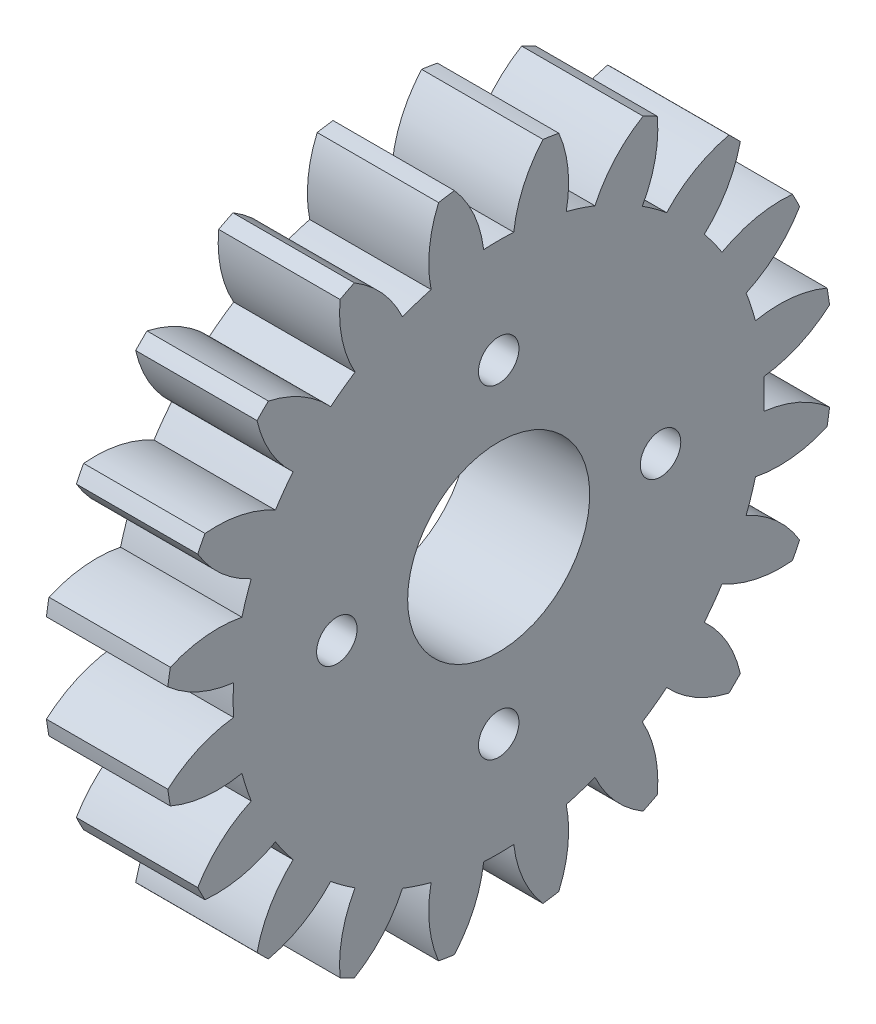
SolidWorks part; units mm, degrees
ref_plane "Plane1" through (0, 0, 0) normal (0, 0, 1) x (1, 0, 0)
ref_plane "Plane2" through (0, 0, 0) normal (0, 1, 0) x (1, 0, 0)
ref_plane "Plane3" through (0, 0, 0) normal (1, 0, 0) x (0, 0, -1)
sketch "HoldingSke" plane through (0, 0, 0) normal (0, 1, 0) x (1, 0, 0)
  line L0 (0, 0) -> (0.6265, -0.228)
  line L1 (-15, 0) -> (100, 0) construction
  line L2 (0, 0) -> (-2.1039, 2.3779)
  line L3 (0, 0) -> (-11.863, 4.5341)
  line L4 (0, 0) -> (8.1152, 2.9537)
  line L5 (0, 0) -> (-46.8476, -17.4728)
  line L6 (0, 0) -> (-4.9738, -3.3558)
  line L7 (-2.1039, 2.3779) -> (8.6586, 51.2059)
  line L8 (-76.2, 54.61) -> (-74.8, 54.61)
  line L9 (-71.009, 38.7566) -> (-53.1078, 45.2721)
  line L10 (-76.2, 71.12) -> (104.1128, 71.12)
  line L11 (0, 0) -> (-6, 0)
  line L12 (-76.2, 101.6) -> (-76.147, 101.6)
  line L13 (24.9733, 27.94) -> (52.9518, 28.4284)
  line L14 (24.9733, 27.94) -> (24.9743, 27.94)
  line L15 (24.9733, 27.94) -> (100.4006, 29.5858)
  line L16 (-63.627, -1.5) -> (-12.827, -1.5)
  circle A0 centre (0, 0) radius 4.5
  circle A1 centre (0, 0) radius 13.124
  circle A2 centre (0, 0) radius 37.5
  circle A3 centre (0, 0) radius 4.5
  dimension "MHD" = 26.248
  dimension "Hub_dia" = 75
  dimension "Bore" = 9
  dimension "MBD" = 9
  dimension "Num_teeth" = 20
  dimension "Pitch" = 0.6667
  dimension "Overall_len" = 50
  dimension "Show_teeth" = 20
  dimension "Thickness" = 6
  dimension "OAL" = 50.0001
  dimension "T_dim" = 1.4
  dimension "Ap" = 20
  dimension "H" = 19.05
  dimension "Pitch_radius" = 180.3128
  dimension "Width" = 6
  dimension "Backlash" = 0.053
  dimension "Addendum_fac" = 1
  dimension "Dedendum_fac" = 1.25
  dimension "Clearance_fac" = 0.25
  dimension "Dedendum_add" = 0.001
  dimension "Module" = 1.5
sketch "BasProSke" plane through (0, 0, 0) normal (0, 1, 0) x (1, 0, 0)
  line L0 (-10, 0) -> (60, 0) construction
  line L1 (0, 0) -> (0, 16.5)
  line L2 (0, 0) -> (6, 0)
  line L3 (6, 0) -> (6, 16.5)
  line L4 (6, 16.5) -> (0, 16.5)
  dimension "Thickness" = 6
  dimension "Diameter" = 33
revolve "Base-Revolve" add sketch "BasProSke" angle 360 about L0
sketch "TooCutSke" plane through (0, 0, 0) normal (1, 0, 0) x (0, 0, -1)
  line L1 (0, 0) -> (0, 107) construction
  line L2 (0, 0) -> (-1.2696, 14.9462) construction
  line L3 (0, 0) -> (-4.6808, 29.5532) construction
  line L4 (-1.2696, 14.9462) -> (-2.3404, 14.7766) construction
  arc A0 (0.7438, 13.1029) -> (-0.7438, 13.1029) centre (0, 0) ccw
  arc A1 (2.21, 16.377) -> (-2.21, 16.377) centre (0, 0) ccw
  circle A2 centre (0, 0) radius 15 construction
  circle A3 centre (0, 0) radius 14.0954 construction
  arc A4 (-0.7438, 13.1029) -> (-2.21, 16.377) centre (-6.7025, 12.3999) ccw
  arc A5 (2.21, 16.377) -> (0.7438, 13.1029) centre (6.7025, 12.3999) ccw
  dimension "Root_dia" = 26.248
  dimension "Overcut_dia" = 33.0508
  dimension "Pitch_dia" = 30
  dimension "Base_dia" = 28.1908
  dimension "Flank_rad" = 6
  dimension "Half_ang" = 9
  dimension "Half_CT" = 1.0841
extrude "ToothCut" cut sketch "TooCutSke" along normal through all
fillet "Breaks" [suppressed] radius 0.03
fillet "RootFillets" [suppressed] radius 0.376
pattern_circular "TeethCuts" count 20 every 18 about axis through (-10, 0, 0) along (1, 0, 0) of "ToothCut", "RootFillets", "Breaks"
sketch "HubNeaOneSke" plane through (0, 0, 0) normal (-1, 0, 0) x (0, 0, 1)
  circle A0 centre (0, 0) radius 13.124
  dimension "Diameter" = 26.248
extrude "HubNearOne" [suppressed] add sketch "HubNeaOneSke" along normal blind 44.0001
sketch "HubNeaBotSke" plane through (0, 0, 0) normal (-1, 0, 0) x (0, 0, 1)
  circle A0 centre (0, 0) radius 13.124
  dimension "Diameter" = 26.248
extrude "HubNearBoth" [suppressed] add sketch "HubNeaBotSke" along normal blind 22
ref_plane "FarPln" through (6, 0, 0) normal (1, 0, 0) x (0, 0, -1)
sketch "HubFarSke" plane through (6, 0, 0) normal (1, 0, 0) x (0, 0, -1)
  circle A0 centre (0, 0) radius 13.124
  dimension "Diameter" = 26.248
extrude "HubFar" [suppressed] add sketch "HubFarSke" along normal blind 22
sketch "BorSke" plane through (0, 0, 0) normal (1, 0, 0) x (0, 0, -1)
  circle A0 centre (0, 0) radius 4.5
  dimension "Diameter" = 9
extrude "Bore" cut sketch "BorSke" along normal mid plane 100.0001
sketch "KeySke" plane through (0, 0, 0) normal (1, 0, 0) x (0, 0, -1)
  line L0 (-1.5, 0) -> (-1.5, 5.9)
  line L1 (-1.5, 5.9) -> (1.5, 5.9)
  line L2 (1.5, 5.9) -> (1.5, 0)
  line L3 (0, 0) -> (0, 34) construction
  line L4 (-1.5, 0) -> (1.5, 0)
  dimension "Offset" = 5.9
  dimension "Width" = 3
extrude "Keyway" [suppressed] cut sketch "KeySke" along normal mid plane 100.0001
pattern_circular "Keyway2" [suppressed] count 2 every 90 about axis through (-10, 0, 0) along (1, 0, 0)
sketch "Esquisse1" plane through (6, 0, 0) normal (1, 0, 0) x (0, 0, -1)
  circle A0 centre (0, 0) radius 15
  dimension "D1" = 30
sketch "Esquisse2" plane through (6, 0, 0) normal (1, 0, 0) x (0, 0, -1)
  circle A0 centre (0, 0) radius 4 construction
  circle A1 centre (0, 0) radius 8 construction
  circle A2 centre (0, 8) radius 1
  circle A3 centre (8, 0) radius 1
  circle A4 centre (0, -8) radius 1
  circle A5 centre (-8, 0) radius 1
  dimension "D1" = 8
  dimension "D2" = 16
  dimension "D3" = 2
  dimension "D4" = 2
  dimension "D5" = 2
  dimension "D6" = 2
extrude "Enlèv. mat.-Extru.1" cut sketch "Esquisse2" against normal blind 6
equation "' \"Module@HoldingSke\" = 6.35"
equation "' \"Num_teeth@HoldingSke\" = 12"
equation "' \"Ap@HoldingSke\" =  20"
equation "' \"Ap@HoldingSke\" = 20"
equation "' \"Width@HoldingSke\" = 0.5 * 25.4"
equation "' \"Hub_dia@HoldingSke\"= 1 * 25.4"
equation "' \"Hub_dia@HoldingSke\" = 1 * 25.4"
equation "' \"Overall_len@HoldingSke\" = 1.0 * 25.4"
equation "' \"Bore@HoldingSke\" = 0.75 * 25.4"
equation "' \"T_dim@HoldingSke\" = 0.1 * 25.4"
equation "' \"Width@KeySke\" = 0.25 * 25.4"
equation "' \"Show_teeth@HoldingSke\" = 13"
equation "' \"Backlash@HoldingSke\" = 0.009 * 25.4"
equation "' \"Addendum_fac@HoldingSke\" = 1.0"
equation "' \"Dedendum_fac@HoldingSke\" = 1.25"
equation "' \"Dedendum_add@HoldingSke\" = 0.00005 * 25.4"
equation "' \"Clearance_fac@HoldingSke\" = 0.25"
equation "\"Pitch@HoldingSke\" = 1 / \"Module@HoldingSke\""
equation "\"Overcut_dia@TooCutSke\" = (\"Num_teeth@HoldingSke\" + 2 * \"Addendum_fac@HoldingSke\") / \"Pitch@HoldingSke\" + 0.002 * 25.4"
equation "\"Pitch_dia@TooCutSke\" = \"Num_teeth@HoldingSke\" / \"Pitch@HoldingSke\""
equation "\"Base_dia@TooCutSke\" = \"Num_teeth@HoldingSke\" / \"Pitch@HoldingSke\" * cos((\"Ap@HoldingSke\"  * 3.14159265 / 180))"
equation "\"Root_dia@TooCutSke\" = (\"Num_teeth@HoldingSke\" + 2) / \"Pitch@HoldingSke\" - 2 * (\"Addendum_fac@HoldingSke\" + \"Dedendum_fac@HoldingSke\") / \"Pitch@HoldingSke\" - \"Dedendum_add@HoldingSke\" * 2"
equation "\"Half_ang@TooCutSke\" = 180 / \"Num_teeth@HoldingSke\""
equation "\"Half_CT@TooCutSke\" = \"Num_teeth@HoldingSke\" / \"Pitch@HoldingSke\" * sin((3.14159265 / 2 / \"Num_teeth@HoldingSke\")) / 2 - 7 * \"Backlash@HoldingSke\" / 4"
equation "\"Flank_rad@TooCutSke\" = \"Num_teeth@HoldingSke\" / \"Pitch@HoldingSke\" / 5"
equation "\"Radius@RootFillets\" = \"Clearance_fac@HoldingSke\" / \"Pitch@HoldingSke\" + \"Dedendum_add@HoldingSke\""
equation "\"Break_rad@Breaks\" = 0.02 / \"Pitch@HoldingSke\""
equation "\"Thickness@HoldingSke\" = \"Width@HoldingSke\""
equation "\"OAL@HoldingSke\" = \"Thickness@HoldingSke\""
equation "\"MHD@HoldingSke\" = (\"Num_teeth@HoldingSke\" + 2) / \"Pitch@HoldingSke\" - 2 * (\"Addendum_fac@HoldingSke\" + \"Dedendum_fac@HoldingSke\")  / \"Pitch@HoldingSke\" - \"Dedendum_add@HoldingSke\" * 2"
equation "\"MBD@HoldingSke\" = (\"Num_teeth@HoldingSke\" + 2) / \"Pitch@HoldingSke\" - 2 * (\"Addendum_fac@HoldingSke\" + \"Dedendum_fac@HoldingSke\")  / \"Pitch@HoldingSke\" - \"Dedendum_add@HoldingSke\" * 2 - 0.002 * 25.4"
equation "\"MHD@HoldingSke\" = ((sgn( \"MHD@HoldingSke\" - \"Hub_dia@HoldingSke\" )-1)*( \"MHD@HoldingSke\" - \"Hub_dia@HoldingSke\" ))/-2+ \"Hub_dia@HoldingSke\""
equation "\"MBD@HoldingSke\" = ((sgn( \"MBD@HoldingSke\" - \"Bore@HoldingSke\" )-1)*( \"MBD@HoldingSke\" - \"Bore@HoldingSke\" ))/-2+ \"Bore@HoldingSke\""
equation "\"OAL@HoldingSke\" = ((sgn( \"OAL@HoldingSke\" - \"Overall_len@HoldingSke\" )+1)*( \"OAL@HoldingSke\" - \"Overall_len@HoldingSke\" ))/2 + \"Overall_len@HoldingSke\" + 0.000002 * 25.4"
equation "\"Num_teeth@TeethCuts\" = int( \"Show_teeth@HoldingSke\" ) + 1"
equation "\"Num_teeth@TeethCuts\" = ((sgn( \"Num_teeth@TeethCuts\" - \"Num_teeth@HoldingSke\" )-1)*( \"Num_teeth@TeethCuts\" - \"Num_teeth@HoldingSke\" ))/-2+ \"Num_teeth@HoldingSke\""
equation "\"Num_teeth@TeethCuts\" = ((sgn( \"Num_teeth@TeethCuts\" - 2.0)+1)*( \"Num_teeth@TeethCuts\" - 2.0))/2 +2.0"
equation "\"Angle@TeethCuts\" = 360.0 / \"Num_teeth@HoldingSke\""
equation "\"Diameter@BasProSke\" = (\"Num_teeth@HoldingSke\" + 2 * \"Addendum_fac@HoldingSke\") / \"Pitch@HoldingSke\""
equation "\"Thickness@BasProSke\"  = \"Thickness@HoldingSke\""
equation "' \"Fillet_rad@BasProSke\" =  \"Thickness@HoldingSke\" * 0.05"
equation "' \"Fillet_rad@BasProSke\" = \"Thickness@HoldingSke\" * 0.05"
equation "\"MHD@HoldingSke\" = ((sgn( \"MHD@HoldingSke\" - \"Root_dia@TooCutSke\" )-1)*( \"MHD@HoldingSke\" - \"Root_dia@TooCutSke\" ))/-2+ \"Root_dia@TooCutSke\""
equation "\"Diameter@HubNeaOneSke\" = \"MHD@HoldingSke\""
equation "\"Length@HubNearOne\" = \"OAL@HoldingSke\" - \"Thickness@BasProSke\""
equation "\"Diameter@HubNeaBotSke\" = \"MHD@HoldingSke\""
equation "\"Length@HubNearBoth\" = ( \"OAL@HoldingSke\" - \"Thickness@BasProSke\" ) / 2.0"
equation "\"Thickness@FarPln\" = \"Thickness@BasProSke\""
equation "\"Diameter@HubFarSke\" = \"MHD@HoldingSke\""
equation "\"Length@HubFar\" = ( \"OAL@HoldingSke\" - \"Thickness@BasProSke\" ) / 2.0"
equation "\"Diameter@BorSke\" = \"MBD@HoldingSke\""
equation "\"D1@Bore\" = \"OAL@HoldingSke\" * 2.0"
equation "\"D1@Keyway\" = \"OAL@HoldingSke\" * 2.0"
equation "\"Offset@KeySke\" = \"T_dim@HoldingSke\" + \"MBD@HoldingSke\" / 2.0"
